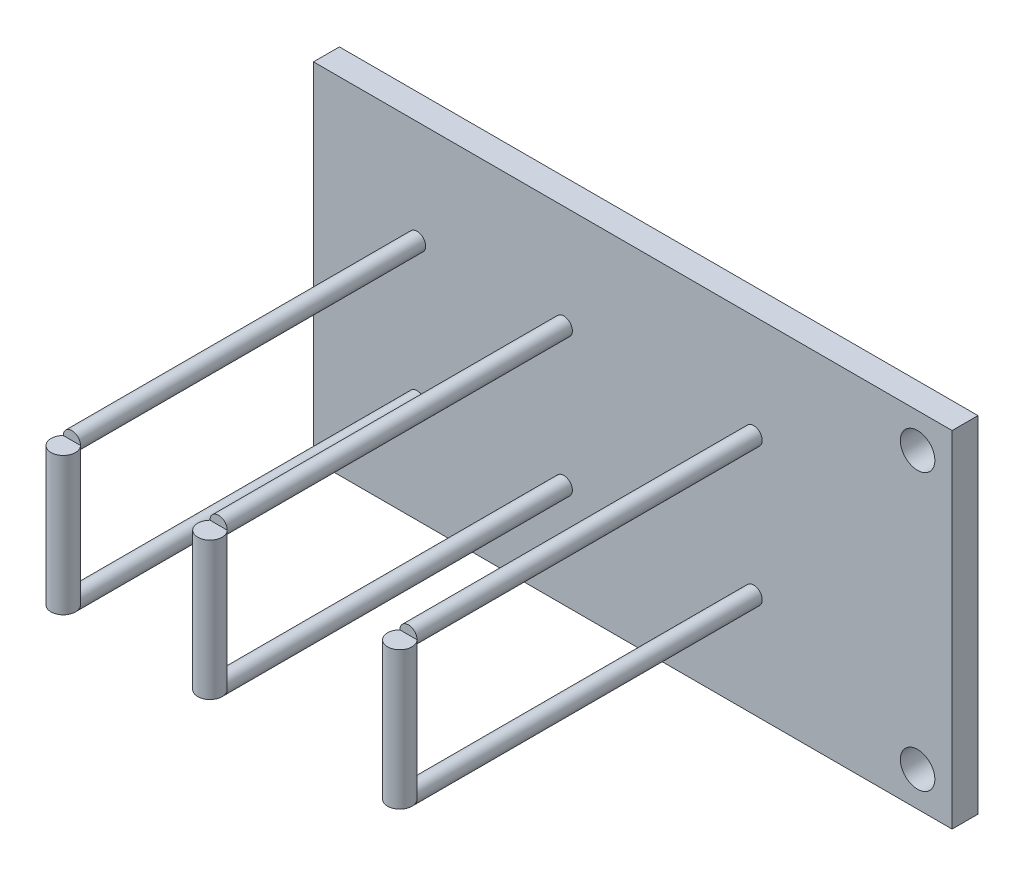
SolidWorks part; units mm, degrees
ref_plane "Plano frontal" through (0, 0, 0) normal (0, 0, 1) x (1, 0, 0)
ref_plane "Plano superior" through (0, 0, 0) normal (0, 1, 0) x (1, 0, 0)
ref_plane "Plano direito" through (0, 0, 0) normal (1, 0, 0) x (0, 0, -1)
sketch "Esboço1" plane through (0, 0, 0) normal (0, 0, 1) x (1, 0, 0)
  line L1 (-18.5, -10) -> (18.5, -10)
  line L2 (-18.5, -10) -> (-18.5, 10)
  line L3 (-18.5, 10) -> (18.5, 10)
  line L4 (18.5, -10) -> (18.5, 10)
  line L5 (-18.5, -10) -> (18.5, 10) construction
  line L6 (-18.5, 10) -> (18.5, -10) construction
  point P0 (0, 0)
  dimension "D1" = 20
  dimension "D2" = 37
extrude "Ressalto-extrusão1" add sketch "Esboço1" along normal blind 1.5
sketch "Esboço2" plane through (0, 0, 1.5) normal (0, 0, 1) x (1, 0, 0)
  line L0 (0, 0) -> (20.494, 0) construction
  line L1 (0, -8) -> (20.494, -8) construction
  line L2 (0, 8) -> (20.494, 8) construction
  line L5 (16.5, -10) -> (16.5, 10)
  line L6 (16.5, -10) -> (16.5, 10) construction
  circle A0 centre (16.5, 8) radius 1
  circle A1 centre (16.5, -8) radius 1
  dimension "D4" = 2
  dimension "D5" = 2
  dimension "D1" = 8
  dimension "D2" = 8
  dimension "D3" = 2
extrude "Corte-extrusão1" cut sketch "Esboço2" against normal through all
sketch "Esboço3" plane through (0, 0, 1.5) normal (0, 0, 1) x (1, 0, 0)
  line L1 (-4, 10) -> (-4, -10) construction
  line L2 (-12.5, 10) -> (-12.5, -10)
  line L3 (-12.5, 10) -> (-12.5, -10) construction
  line L4 (7, 10) -> (7, -10) construction
  line L5 (-18.5, 0) -> (18.5, 0) construction
  line L6 (-18.5, 10) -> (-18.5, -10) construction
  line L7 (18.5, -10) -> (18.5, 10) construction
  line L8 (-18.5, -4) -> (18.5, -4) construction
  line L9 (-18.5, 4) -> (18.5, 4) construction
  circle A0 centre (-12.5, 4) radius 0.5
  circle A1 centre (-4, 4) radius 0.5
  circle A2 centre (7, 4) radius 0.5
  circle A3 centre (7, -4) radius 0.5
  circle A4 centre (-4, -4) radius 0.5
  circle A5 centre (-12.5, -4) radius 0.5
  dimension "D6" = 1
  dimension "D1" = 6
  dimension "D2" = 8.5
  dimension "D3" = 11
  dimension "D4" = 4
  dimension "D5" = 4
extrude "Ressalto-extrusão2" add sketch "Esboço3" along normal blind 20
sketch "Esboço4" plane through (0, 0, 21.5) normal (0, 0, 1) x (1, 0, 0)
  line L1 (-13, 4) -> (-12, 4)
  line L2 (-13, 4) -> (-13, -4)
  line L3 (-13, -4) -> (-12, -4)
  line L4 (-12, 4) -> (-12, -4)
  line L5 (-4.5, 4) -> (-3.5, 4)
  line L6 (-4.5, 4) -> (-4.5, -4)
  line L7 (-4.5, -4) -> (-3.5, -4)
  line L8 (-3.5, 4) -> (-3.5, -4)
  line L9 (6.5, 4) -> (7.5, 4)
  line L10 (6.5, 4) -> (6.5, -4)
  line L11 (6.5, -4) -> (7.5, -4)
  line L12 (7.5, 4) -> (7.5, -4)
  circle A0 centre (-12.5, 4) radius 0.5 construction
  circle A1 centre (-12.5, 4) radius 0.5 construction
  circle A2 centre (-12.5, -4) radius 0.5 construction
  circle A3 centre (-4, 4) radius 0.5 construction
  circle A4 centre (-4, 4) radius 0.5 construction
  circle A5 centre (-4, -4) radius 0.5 construction
  circle A6 centre (7, 4) radius 0.5 construction
  circle A7 centre (7, 4) radius 0.5 construction
  circle A8 centre (7, -4) radius 0.5 construction
extrude "Ressalto-extrusão3" add sketch "Esboço4" along normal blind 1
sketch "Esboço5" plane through (0, -4, 0) normal (0, -1, 0) x (1, 0, 0)
  circle A0 centre (-12.5, 22) radius 0.7071
  circle A1 centre (-4, 22) radius 0.7071
  circle A2 centre (7, 22) radius 0.7071
extrude "Ressalto-extrusão4" add sketch "Esboço5" against normal up to surface (8 mm away) up to face at (-4, 4, 22)
